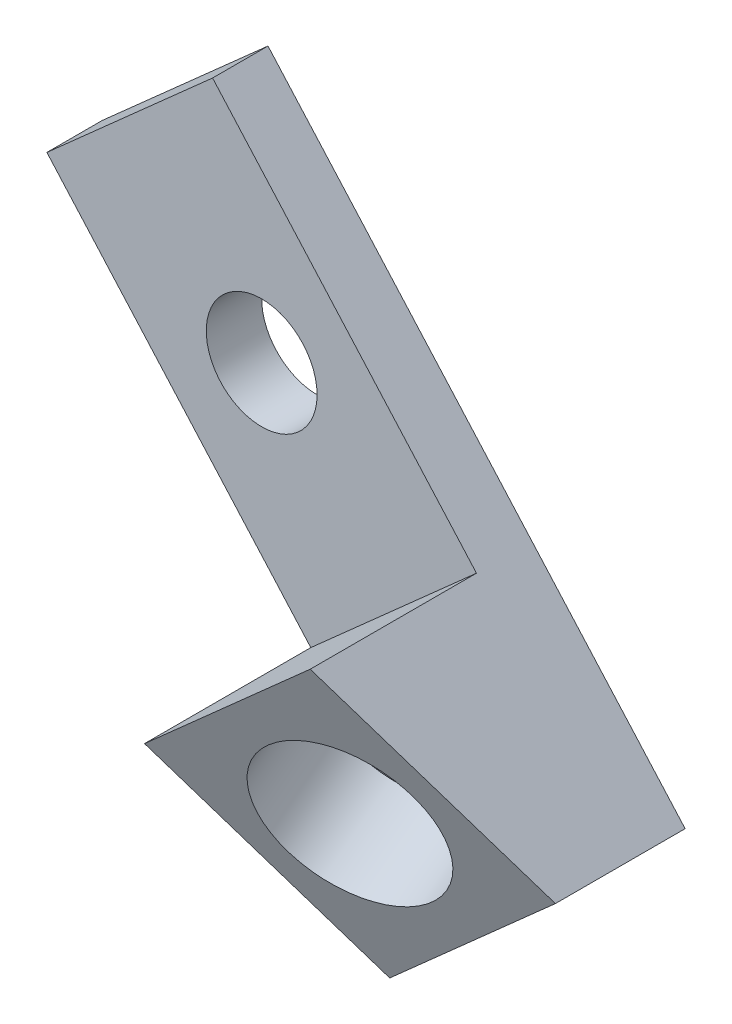
SolidWorks part; units mm, degrees
ref_plane "Front" through (0, 0, 0) normal (0, 0, 1) x (1, 0, 0)
ref_plane "Top" through (0, 0, 0) normal (0, 1, 0) x (1, 0, 0)
ref_plane "Right" through (0, 0, 0) normal (1, 0, 0) x (0, 0, -1)
ref_plane "Plane1" through (0, 0, 457.2) normal (0, 0, 1) x (1, 0, 0)
sketch "Sketch1" plane through (0, 0, 0) normal (0, 0, 1) x (1, 0, 0)
  line L0 (0, 0) -> (-88.9, 0) construction
  line L1 (-88.9, 0) -> (-228.6, 157.1625) construction
  line L2 (-88.9, 0) -> (-228.6, -85.725) construction
  point P3 (-231.3954, 157.1625)
  point P6 (-282.6715, -85.725)
  dimension "D1" = 88.9
  dimension "D2" = 85.725
  dimension "D3" = 242.8875
  dimension "D4" = 228.6
sketch "Sketch2" plane through (0, 0, 457.2) normal (0, 0, 1) x (1, 0, 0)
  point P0 (-88.9, 0)
  point P1 (0, 0)
sketch3d "3DSketch1"
  line L0 (-88.9, 0, 457.2) -> (-210.0377, 136.2799, 0)
  line L1 (-88.9, 0, 0) -> (-228.6, 157.1625, 0) construction
  dimension "D1" = 27.94
ref_plane "Plane2" through (-49.6614, -44.1434, 0) normal (-0.7474, -0.6644, 0) x (0, 0, 1)
sketch "Sketch3" plane through (-49.6614, -44.1434, 0) normal (-0.7474, -0.6644, 0) x (0, 0, 1)
  line L0 (0, 292.0946) -> (0, 220.1578)
  line L1 (0, 59.0619) -> (0, 269.3383) construction
  line L2 (0, 220.1578) -> (14.8618, 220.1578)
  line L3 (14.8618, 220.1578) -> (25.4, 246.5819)
  line L4 (25.4, 246.5819) -> (6.35, 246.5819)
  line L5 (6.35, 246.5819) -> (6.35, 292.0946)
  line L6 (6.35, 292.0946) -> (0, 292.0946)
  line L7 (457.2, 59.0619) -> (0, 241.3983) construction
  line L8 (6.35, 269.3383) -> (0, 269.3383) construction
  point P10 (14.8618, 222.5292)
  point P14 (20.1309, 233.3699)
  dimension "D1" = 28.448
  dimension "D2" = 6.35
  dimension "D3" = 25.4
  dimension "D4" = 27.94
extrude "Boss-Extrude1" add sketch "Sketch3" along normal mid plane 25.4
sketch "Sketch4" plane through (0, 0, 6.35) normal (0, 0, 1) x (1, 0, 0)
  line L0 (-243.7185, 174.1708) -> (-228.6, 157.1625) construction
  line L1 (-253.2106, 165.7334) -> (-234.2264, 182.6082) construction
  line L2 (-228.6, 157.1625) -> (-219.1079, 165.5999) construction
  line L3 (-203.9894, 148.5916) -> (-234.2264, 182.6082) construction
  circle A0 centre (-228.6, 157.1625) radius 6.35
  point P3 (-226.4455, 157.1625)
  dimension "D1" = 12.7
extrude "Cut-Extrude1" cut sketch "Sketch4" against normal through all
sketch "Sketch5" plane through (-16.6738, 18.758, -62.9305) normal (0.2461, -0.2769, 0.9289) x (0.9692, 0.0703, -0.2359)
  line L0 (-203.053, 141.57) -> (-193.9969, 130.6014) construction
  line L1 (-212.8463, 133.4841) -> (-193.2597, 149.6558) construction
  line L2 (-193.9969, 130.6014) -> (-184.2036, 138.6873) construction
  line L3 (-175.1474, 127.7188) -> (-193.2597, 149.6558) construction
  circle A0 centre (-193.9969, 130.6014) radius 9.525
  dimension "D1" = 19.05
extrude "Cut-Extrude2" cut sketch "Sketch5" against normal blind 11.43
